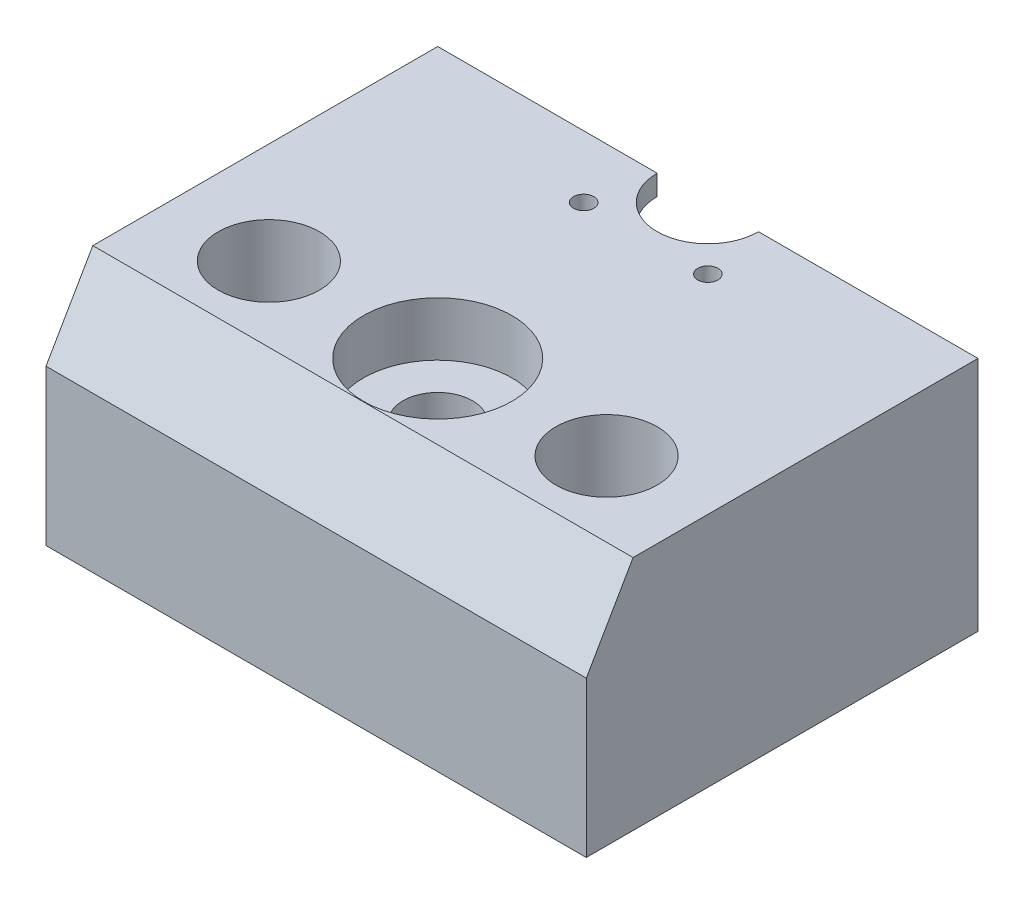
SolidWorks part; units mm, degrees
ref_plane "Front Plane" through (0, 0, 0) normal (0, 0, 1) x (1, 0, 0)
ref_plane "Top Plane" through (0, 0, 0) normal (0, 1, 0) x (1, 0, 0)
ref_plane "Right Plane" through (0, 0, 0) normal (1, 0, 0) x (0, 0, -1)
sketch "Sketch1" plane through (0, 0, 0) normal (0, 1, 0) x (1, 0, 0)
  line L0 (19.15, 0) -> (40, 0)
  line L1 (-40, 0) -> (-19.15, 0)
  line L2 (-40, 0) -> (-40, -58)
  line L3 (-40, -58) -> (40, -58)
  line L4 (40, 0) -> (40, -58)
  arc A0 (-19.15, 0) -> (19.15, 0) centre (0, 0) ccw
  point P9 (0, -58)
  dimension "D1" = 19.15
  dimension "D2" = 80
  dimension "D3" = 58
extrude "Boss-Extrude1" add sketch "Sketch1" along normal blind 35
sketch "Sketch2" plane through (0, 35, 0) normal (0, 1, 0) x (1, 0, 0)
  line L0 (0, 0) -> (0, -58) construction
  line L5 (-40, -58) -> (40, -58) construction
  circle A0 centre (-25, -40) radius 7.5
  circle A1 centre (25, -40) radius 7.5
  circle A2 centre (0, -40) radius 5.15
  dimension "D1" = 15
  dimension "D3" = 10.3
  dimension "D2" = 50
extrude "Cut-Extrude1" cut sketch "Sketch2" against normal through all
sketch "Sketch5" plane through (0, 35, 0) normal (0, 1, 0) x (1, 0, 0)
  line L0 (-19.15, 0) -> (-7.5, 0)
  line L1 (7.5, 0) -> (19.15, 0)
  arc A1 (7.5, 0) -> (-7.5, 0) centre (0, 0) cw
  arc A2 (-19.15, 0) -> (19.15, 0) centre (0, 0) ccw
  arc A3 (-19.15, 0) -> (19.15, 0) centre (0, 0) ccw
  dimension "D2" = 7.5
  dimension "D1" = 0
extrude "Boss-Extrude2" add sketch "Sketch5" against normal blind 3
sketch "Sketch6" plane through (0, 32, 0) normal (0, -1, 0) x (1, 0, 0)
  line L0 (0, 0) -> (9.1924, 9.1924) construction
  line L2 (0, 0) -> (0, 19.15) construction
  circle A0 centre (9.1924, 9.1924) radius 1.5
  arc A1 (19.15, 0) -> (-19.15, 0) centre (0, 0) ccw construction
  circle A2 centre (-9.1924, 9.1924) radius 1.5
  dimension "D1" = 3
  dimension "D2" = 13
  dimension "D3" = 45
extrude "Cut-Extrude3" cut sketch "Sketch6" against normal through all
chamfer "Chamfer1" distance 12 angle 30 1 edges at (0, 35, 58)
sketch "Sketch7" plane through (0, 35, 0) normal (0, 1, 0) x (1, 0, 0)
  circle A0 centre (0, -40) radius 11
  dimension "D1" = 22
extrude "Cut-Extrude4" cut sketch "Sketch7" against normal blind 8
